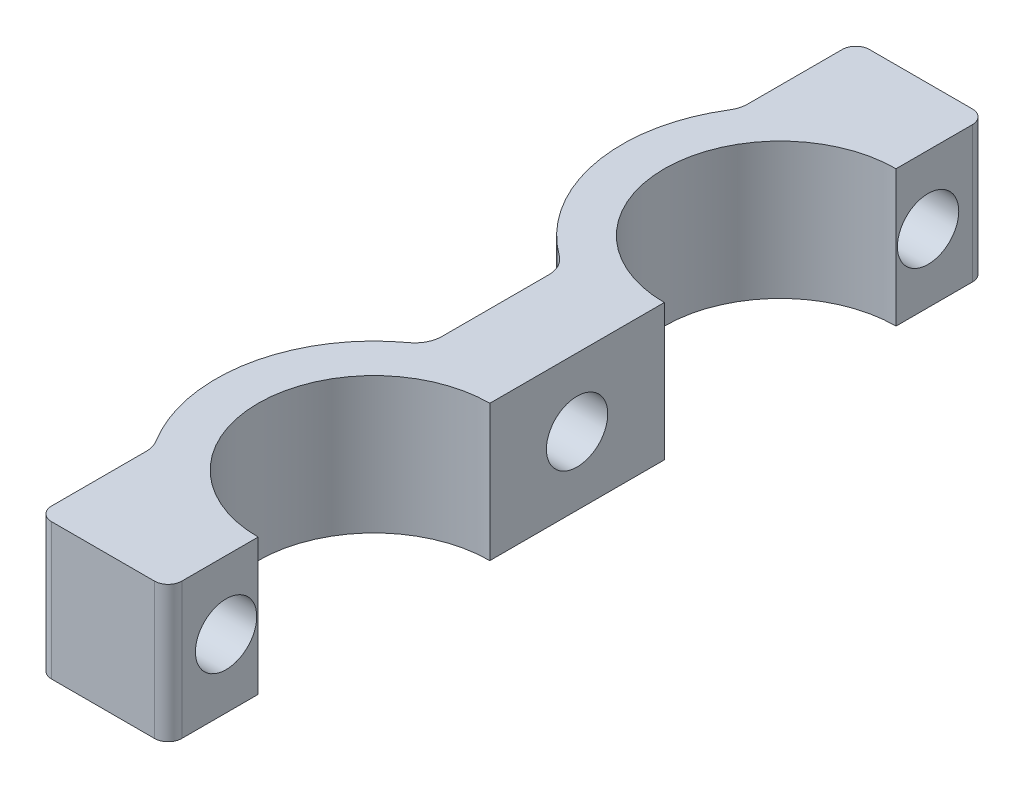
SolidWorks part; units mm, degrees
material "3.1355 (EN-AW 2024)"
ref_plane "Front" through (0, 0, 0) normal (0, 0, 1) x (1, 0, 0)
ref_plane "Top" through (0, 0, 0) normal (0, 1, 0) x (1, 0, 0)
ref_plane "Right" through (0, 0, 0) normal (1, 0, 0) x (0, 0, -1)
sketch "Эскиз1" plane through (0, 0, 0) normal (0, 1, 0) x (1, 0, 0)
  line L0 (0, 0) -> (0, 60) construction
  line L1 (0, 30) -> (-15.0292, 30) construction
  line L2 (0, 0) -> (0, 8)
  line L3 (0, 60) -> (0, 52)
  line L4 (0, 37.8) -> (0, 22.2)
  line L5 (-3, 0) -> (-3, 5.4558)
  line L6 (-3, 35.2558) -> (-3, 24.7442)
  line L7 (-3, 60) -> (-3, 54.5442)
  line L8 (-3, 60) -> (0, 60)
  line L9 (-3, 0) -> (0, 0)
  circle A0 centre (0, 15.1) radius 7.1 construction
  circle A1 centre (0, 44.9) radius 7.1 construction
  arc A2 (0, 8) -> (0, 22.2) centre (0, 15.1) cw
  arc A3 (0, 52) -> (0, 37.8) centre (0, 44.9) ccw
  arc A4 (-3, 5.4558) -> (-3, 24.7442) centre (0, 15.1) cw
  arc A5 (-3, 54.5442) -> (-3, 35.2558) centre (0, 44.9) ccw
  point P9 (0, 22.2)
  dimension "D2" = 15.1
  dimension "D3" = 14.2
  dimension "D1" = 60
  dimension "D4" = 3
extrude "Бобышка-Вытянуть1" add sketch "Эскиз1" along normal blind 10
sketch "Эскиз2" plane through (0, 10, 0) normal (0, 1, 0) x (1, 0, 0)
  line L0 (-3, 60) -> (-8.0498, 60)
  line L1 (-8.0498, 60) -> (-8.0498, 51)
  line L2 (-3, 60) -> (-3, 54.5442)
  line L3 (0, 30) -> (-3, 30) construction
  line L4 (0, 22.2) -> (0, 37.8) construction
  line L5 (-3, 35.2558) -> (-3, 24.7442) construction
  line L6 (-3, 0) -> (-3, 5.4558)
  line L7 (-8.0498, 0) -> (-8.0498, 9)
  line L8 (-3, 0) -> (-8.0498, 0)
  arc A0 (-3, 54.5442) -> (-3, 35.2558) centre (0, 44.9) ccw construction
  arc A1 (-3, 54.5442) -> (-8.0498, 51) centre (0, 44.9) ccw
  arc A2 (-3, 5.4558) -> (-8.0498, 9) centre (0, 15.1) cw
  dimension "D1" = 9
sketch "Эскиз3" plane through (0, 0, 0) normal (-1, 0, 0) x (0, 0, 1)
  line L0 (-60, 5) -> (-54.7288, 5) construction
  line L1 (-60, 10) -> (-60, 0) construction
  line L3 (-30, 10) -> (-30, 0) construction
  line L4 (-35.2558, 10) -> (-24.7442, 10) construction
  line L5 (-35.2558, 0) -> (-24.7442, 0) construction
  circle A0 centre (-55.75, 5) radius 2.25
  circle A1 centre (-4.25, 5) radius 2.25
  point P6 (-58, 5)
  point P7 (-53.5, 5)
  dimension "D1" = 4.5
  dimension "D2" = 2
extrude "Бобышка-Вытянуть2" add sketch "Эскиз2" against normal up to surface (10 mm away) up to face at (-3.8667, 0, -30)
sketch "Эскиз9" plane through (0, 0, 0) normal (0, -1, 0) x (1, 0, 0)
  line L1 (-8.0498, -9) -> (-8.0498, 0) construction
  line L2 (-6, -35.2558) -> (-6, -24.7442)
  line L3 (-6, -34.9723) -> (-6, -25.0277)
  line L4 (-8.0498, 0) -> (-8.0498, -9)
  line L6 (-9.5498, -60) -> (-8.0498, -60)
  line L7 (-3, -35.2558) -> (-3, -24.7442) construction
  line L8 (-3, -35.2558) -> (-3, -24.7442)
  line L9 (-8.0498, -9) -> (-8.0498, 0)
  line L10 (-9.5498, -8.5151) -> (-9.5498, 0)
  line L12 (-9.5498, 0) -> (-8.0498, 0)
  line L13 (-9.5498, -60) -> (-9.5498, -51)
  line L14 (-9.5498, -60) -> (-9.5498, -51.4849)
  line L15 (-8.0498, -60) -> (-8.0498, -51)
  line L16 (-9.5498, -9) -> (-9.5498, 0) construction
  arc A2 (-9.2454, -8.0941) -> (-3.4455, -26.1765) centre (0, -15.1) ccw
  arc A3 (-9.5498, -8.5151) -> (-6, -25.0277) centre (0, -15.1) ccw
  arc A4 (-8.0498, -9) -> (-3, -24.7442) centre (0, -15.1) ccw construction
  arc A5 (-3.4455, -33.8235) -> (-9.2454, -51.9059) centre (0, -44.9) ccw
  arc A6 (-6, -34.9723) -> (-9.5498, -51.4849) centre (0, -44.9) ccw
  arc A7 (-3, -35.2558) -> (-8.0498, -51) centre (0, -44.9) ccw construction
  arc A8 (-8.0498, -9) -> (-3, -24.7442) centre (0, -15.1) ccw
  arc A9 (-3, -35.2558) -> (-8.0498, -51) centre (0, -44.9) ccw
  dimension "D1" = 1.5
  dimension "D2" = 1.5
  dimension "D3" = 3
  dimension "D4" = 1.5
  dimension "D5" = 1.5
extrude "Бобышка-Вытянуть4" add sketch "Эскиз9" against normal through all
sketch "Эскиз4" plane through (-6, 0, 0) normal (-1, 0, 0) x (0, 0, 1)
  line L0 (-30, 10) -> (-30, 0) construction
  line L3 (-34.9723, 10) -> (-25.0277, 10) construction
  line L4 (-34.9723, 0) -> (-25.0277, 0) construction
  circle A0 centre (-30, 5) radius 2.25
  dimension "D1" = 4.5
extrude "Вырез-Вытянуть4" cut sketch "Эскиз3" along normal through all
extrude "Вырез-Вытянуть2" cut sketch "Эскиз4" against normal through all
fillet "Скругление2" radius 1 2 edges at (0, 5, 0) (0, 5, -60)
sketch "Эскиз5" plane through (0, 0, 0) normal (0, -1, 0) x (1, 0, 0)
  line L0 (0, -8) -> (0, -8.1)
  line L1 (0, -51.9) -> (0, -52)
  line L2 (0, -37.8) -> (0, -37.9)
  line L3 (0, -22.1) -> (0, -22.2)
  arc A0 (0, -8) -> (0, -22.2) centre (0, -15.1) ccw construction
  arc A1 (0, -37.8) -> (0, -52) centre (0, -44.9) ccw construction
  arc A2 (0, -8) -> (0, -22.2) centre (0, -15.1) ccw
  arc A3 (0, -37.8) -> (0, -52) centre (0, -44.9) ccw
  arc A4 (0, -8.1) -> (0, -22.1) centre (0, -15.1) ccw
  arc A5 (0, -37.9) -> (0, -51.9) centre (0, -44.9) ccw
  dimension "D1" = 0.1
extrude "Бобышка-Вытянуть3" add sketch "Эскиз5" against normal through all
sketch "Эскиз7" plane through (0, 10, 0) normal (0, 1, 0) x (1, 0, 0)
  line L0 (0, 51.9) -> (0, 59) construction
  line L1 (0, 22.1) -> (0, 37.9) construction
  line L2 (0, 1) -> (0, 8.1) construction
  line L3 (0, 51.9) -> (0, 53.4)
  line L4 (0, 22.1) -> (0, 23.6)
  line L5 (0, 6.6) -> (0, 8.1)
  line L6 (0, 36.4) -> (0, 37.9)
  arc A8 (0, 53.4) -> (0, 36.4) centre (0, 44.9) ccw
  arc A9 (0, 53.4) -> (0, 36.4) centre (0, 44.9) ccw
  arc A10 (0, 51.9) -> (0, 37.9) centre (0, 44.9) ccw construction
  arc A11 (0, 23.6) -> (0, 6.6) centre (0, 15.1) ccw
  arc A12 (0, 23.6) -> (0, 6.6) centre (0, 15.1) ccw
  arc A13 (0, 22.1) -> (0, 8.1) centre (0, 15.1) ccw construction
  arc A14 (0, 51.9) -> (0, 37.9) centre (0, 44.9) ccw
  arc A15 (0, 22.1) -> (0, 8.1) centre (0, 15.1) ccw
  dimension "D1" = 1.5
  dimension "D2" = 1.5
extrude "Вырез-Вытянуть3" cut sketch "Эскиз7" against normal through all
fillet "Скругление3" radius 1 2 edges at (-9.5498, 5, 0) (-9.5498, 5, -60)
fillet "Скругление4" radius 2 4 edges at (-6, 5, -34.9723) (-6, 5, -25.0277) (-9.5498, 5, -51.4849) (-9.5498, 5, -8.5151)
equation "\"D2@Эскиз1\"=8+\"D3@Эскиз1\"/2"
